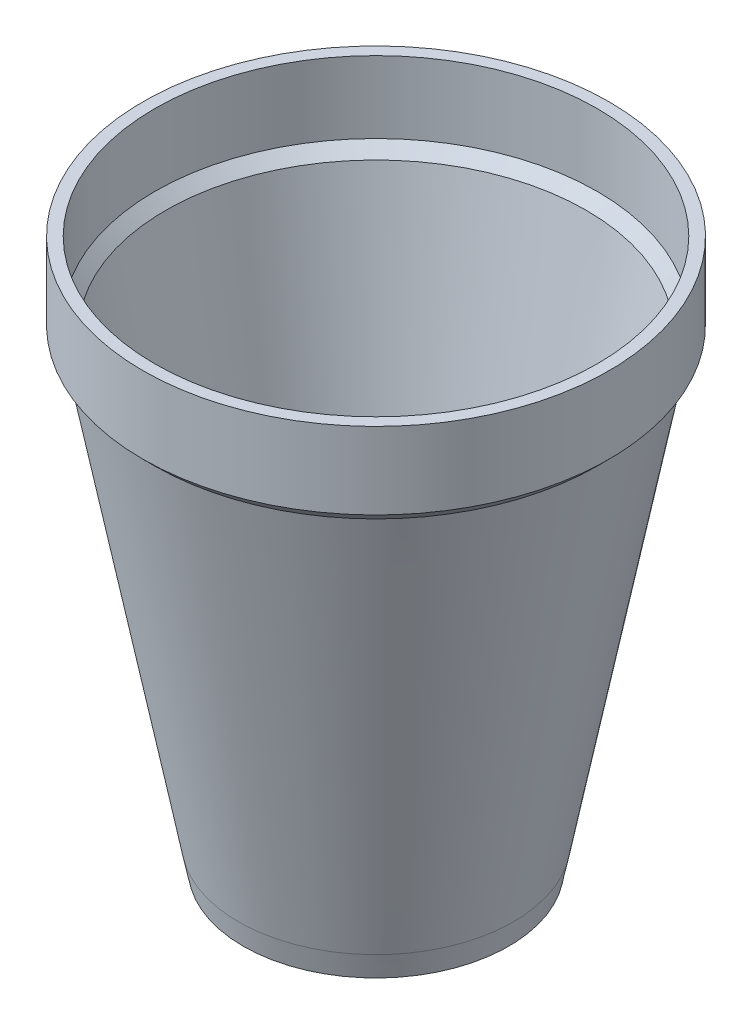
SolidWorks part; units mm, degrees
ref_plane "Alzado" through (0, 0, 0) normal (0, 0, 1) x (1, 0, 0)
ref_plane "Planta" through (0, 0, 0) normal (0, 1, 0) x (1, 0, 0)
ref_plane "Vista lateral" through (0, 0, 0) normal (1, 0, 0) x (0, 0, -1)
sketch "Croquis1" plane through (0, 0, 0) normal (0, 0, 1) x (1, 0, 0)
  line L0 (0, 0) -> (23.32, 0)
  line L1 (0, 0) -> (0, 89)
  line L2 (0, 89) -> (39.5, 89)
  line L3 (39.5, 89) -> (39.5, 76)
  line L6 (37.5, 74) -> (39.5, 76)
  line L7 (37.5, 74) -> (23.32, 0)
  dimension "D1" = 23.32
  dimension "D2" = 89
  dimension "D3" = 39.5
  dimension "D4" = 13
  dimension "D5" = 2
  dimension "D6" = 2
  dimension "D7" = 45
revolve "Revolución4" add sketch "Croquis1" angle 360 about L1
shell "Vaciado4" thickness 2
sketch "Croquis7" plane through (0, 0, 0) normal (0, -1, 0) x (-1, 0, 0)
  circle A0 centre (0, 0) radius 23.32
extrude "Saliente-Extruir3" add sketch "Croquis7" along normal blind 4 draft 11.46
sketch "Croquis8" plane through (0, -4, 0) normal (0, -1, 0) x (-1, 0, 0)
  circle A0 centre (0, 0) radius 20
  dimension "D1" = 40
extrude "Cortar-Extruir1" cut sketch "Croquis8" against normal blind 1 draft 11.46 contours A0 draft outward yes
ref_plane "Plano1" through (0, -3, 0) normal (0, -1, 0) x (-1, 0, 0)
sketch "Croquis10" plane through (0, -3, 0) normal (0, -1, 0) x (-1, 0, 0)
  line L0 (-20, 0) -> (20, 0) construction
  circle A0 centre (0, 0) radius 20 construction
  text T0 "ECOGlass\r\nUNI" font "Century Gothic" height 5
extrude "Cortar-Extruir3" cut sketch "Croquis10" against normal blind 1.5
fillet "Redondeo1" radius 0.5 1 edges at (0, -3, -20.2027)
